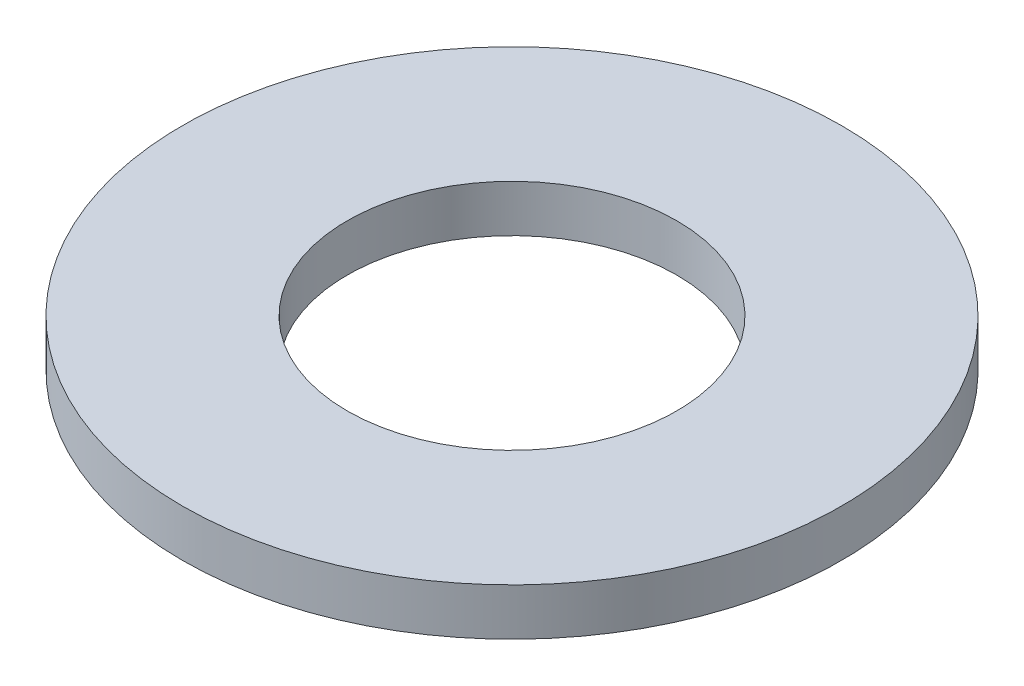
SolidWorks part; units mm, degrees
material "uhlíková ocel 7850"
ref_plane "Přední rovina" through (0, 0, 0) normal (0, 0, 1) x (1, 0, 0)
ref_plane "Horní rovina" through (0, 0, 0) normal (0, 1, 0) x (1, 0, 0)
ref_plane "Pravá rovina" through (0, 0, 0) normal (1, 0, 0) x (0, 0, -1)
sketch "Skica1" plane through (0, 0, 0) normal (0, 1, 0) x (1, 0, 0)
  circle A0 centre (0, 0) radius 3.5
  circle A1 centre (0, 0) radius 1.75
  dimension "D1" = 3.5
  dimension "D2" = 7
extrude "Přidat vysunutím1" add sketch "Skica1" along normal blind 0.5
